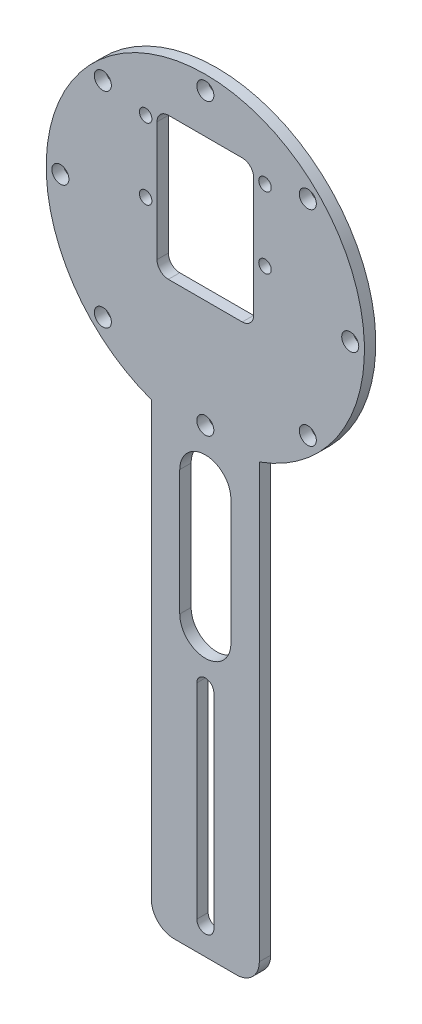
SolidWorks part; units mm, degrees
material "Epoxy, renforcé"
ref_plane "Plan de face" through (0, 0, 0) normal (0, 0, 1) x (1, 0, 0)
ref_plane "Plan de dessus" through (0, 0, 0) normal (0, 1, 0) x (1, 0, 0)
ref_plane "Plan de droite" through (0, 0, 0) normal (1, 0, 0) x (0, 0, -1)
sketch "Esquisse1" plane through (0, 0, 0) normal (0, 0, 1) x (1, 0, 0)
  line L0 (0, 0) -> (0, 100) construction
  line L1 (0, 0) -> (-9.5, 0) construction
  line L2 (9.5, 0) -> (-9.5, 0)
  line L3 (0, 100) -> (0, 134.5) construction
  line L4 (-8.5, 125) -> (8.5, 125)
  line L5 (8.5, 100) -> (-8.5, 100)
  line L6 (-8.5, 100) -> (-8.5, 125)
  line L13 (8.5, 100) -> (8.5, 125)
  line L17 (-10.5, 110.5) -> (-10.5, 123) construction
  line L19 (-9.5, 80.1609) -> (-9.5, 0)
  line L20 (9.5, 80.1609) -> (9.5, 0)
  circle A0 centre (-10.5, 123) radius 1.1
  circle A1 centre (-10.5, 110.5) radius 1.1
  circle A2 centre (10.5, 110.5) radius 1.1
  circle A3 centre (10.5, 123) radius 1.1
  arc A4 (9.5, 80.1609) -> (-9.5, 80.1609) centre (0, 106.5) ccw
  circle A5 centre (0, 132) radius 1.5
  circle A6 centre (18.0312, 124.5312) radius 1.5
  circle A7 centre (25.5, 106.5) radius 1.5
  circle A8 centre (18.0312, 88.4688) radius 1.5
  circle A9 centre (0, 81) radius 1.5
  circle A10 centre (-18.0312, 88.4688) radius 1.5
  circle A11 centre (-25.5, 106.5) radius 1.5
  circle A12 centre (-18.0312, 124.5312) radius 1.5
  point P31 (0, 0)
  point P40 (0, 106.5)
  dimension "D4" = 2.2
  dimension "D9" = 2.2
  dimension "D12" = 56
  dimension "D11" = 3
  dimension "D2" = 100
  dimension "D3" = 2
  dimension "D5" = 2
  dimension "D6" = 12.5
  dimension "D7" = 25
  dimension "D8" = 19
  dimension "D10" = 6.5
  dimension "D13" = 2.5
  dimension "D14" = 17
  dimension "D15" = 8
extrude "Boss.-Extru.1" add sketch "Esquisse1" along normal blind 2
fillet "Congé1" radius 2 4 edges at (-8.5, 100, 1) (8.5, 100, 1) (8.5, 125, 1) (-8.5, 125, 1)
sketch "Esquisse2" plane through (0, 0, 2) normal (0, 0, 1) x (1, 0, 0)
  line L0 (0, 72) -> (0, 50) construction
  line L1 (4.5, 72) -> (4.5, 50)
  line L2 (-4.5, 72) -> (-4.5, 50)
  line L3 (9.5, 0) -> (9.5, 80.1609) construction
  line L4 (6.5, 100) -> (-6.5, 100) construction
  line L6 (-9.5, 0) -> (9.5, 0) construction
  line L7 (0, 41) -> (0, 5) construction
  line L8 (1.5, 41) -> (1.5, 5)
  line L9 (-1.5, 41) -> (-1.5, 5)
  arc A0 (4.5, 72) -> (-4.5, 72) centre (0, 72) ccw
  arc A1 (-4.5, 50) -> (4.5, 50) centre (0, 50) ccw
  arc A2 (1.5, 41) -> (-1.5, 41) centre (0, 41) ccw
  arc A3 (-1.5, 5) -> (1.5, 5) centre (0, 5) ccw
  point P3 (0, 61)
  point P12 (0, 100)
  point P17 (0, 23)
  dimension "D1" = 5
  dimension "D2" = 28
  dimension "D3" = 50
  dimension "D4" = 1.5
  dimension "D5" = 36
  dimension "D6" = 5
extrude "Enlèv. mat.-Extru.1" cut sketch "Esquisse2" against normal blind 2
fillet "Congé2" radius 4 2 edges at (-9.5, 0, 1) (9.5, 0, 1)
